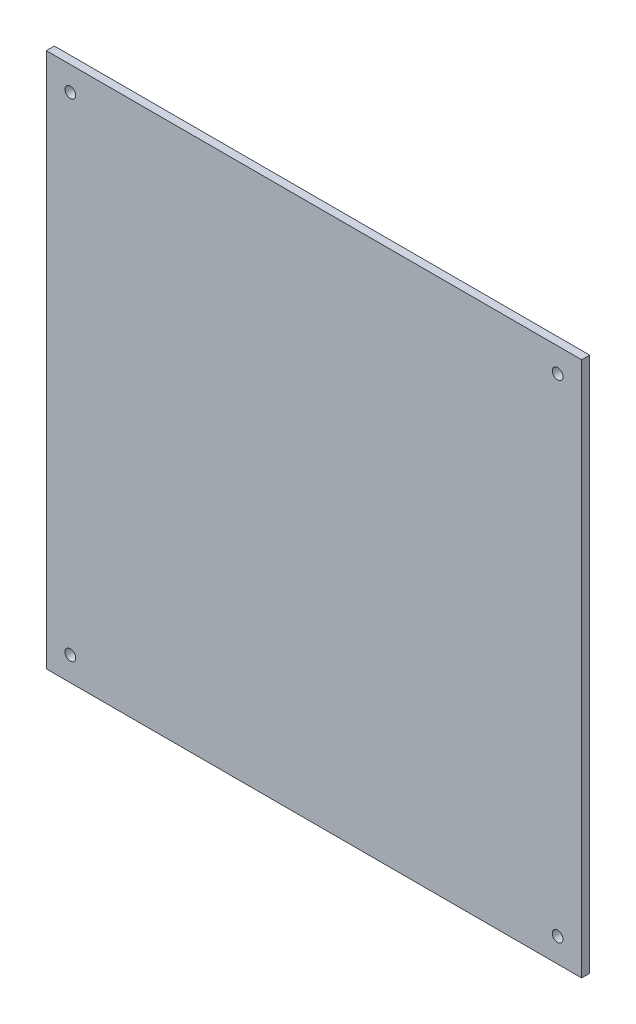
SolidWorks part; units mm, degrees
ref_plane "Plan de face" through (0, 0, 0) normal (0, 0, 1) x (1, 0, 0)
ref_plane "Plan de dessus" through (0, 0, 0) normal (0, 1, 0) x (1, 0, 0)
ref_plane "Plan de droite" through (0, 0, 0) normal (1, 0, 0) x (0, 0, -1)
sketch "Esquisse1" plane through (0, 0, 0) normal (0, 0, 1) x (1, 0, 0)
  line L1 (0, 0) -> (200, 0)
  line L2 (0, 0) -> (0, 200)
  line L3 (0, 200) -> (200, 200)
  line L4 (200, 0) -> (200, 200)
  dimension "D1" = 200
  dimension "D2" = 200
extrude "Boss.-Extru.1" add sketch "Esquisse1" along normal blind 3
sketch "Esquisse2" plane through (0, 0, 3) normal (0, 0, 1) x (1, 0, 0)
  line L0 (100, 200) -> (100, 0) construction
  line L1 (200, 200) -> (0, 200) construction
  line L2 (0, 0) -> (200, 0) construction
  line L3 (0, 100) -> (200, 100) construction
  line L4 (0, 200) -> (0, 0) construction
  line L5 (200, 0) -> (200, 200) construction
  circle A0 centre (9, 191) radius 2
  circle A1 centre (191, 191) radius 2
  circle A2 centre (191, 9) radius 2
  circle A3 centre (9, 9) radius 2
  dimension "D1" = 4
  dimension "D2" = 9
  dimension "D3" = 9
extrude "Enlèv. mat.-Extru.1" cut sketch "Esquisse2" against normal through all both and the other way through all
